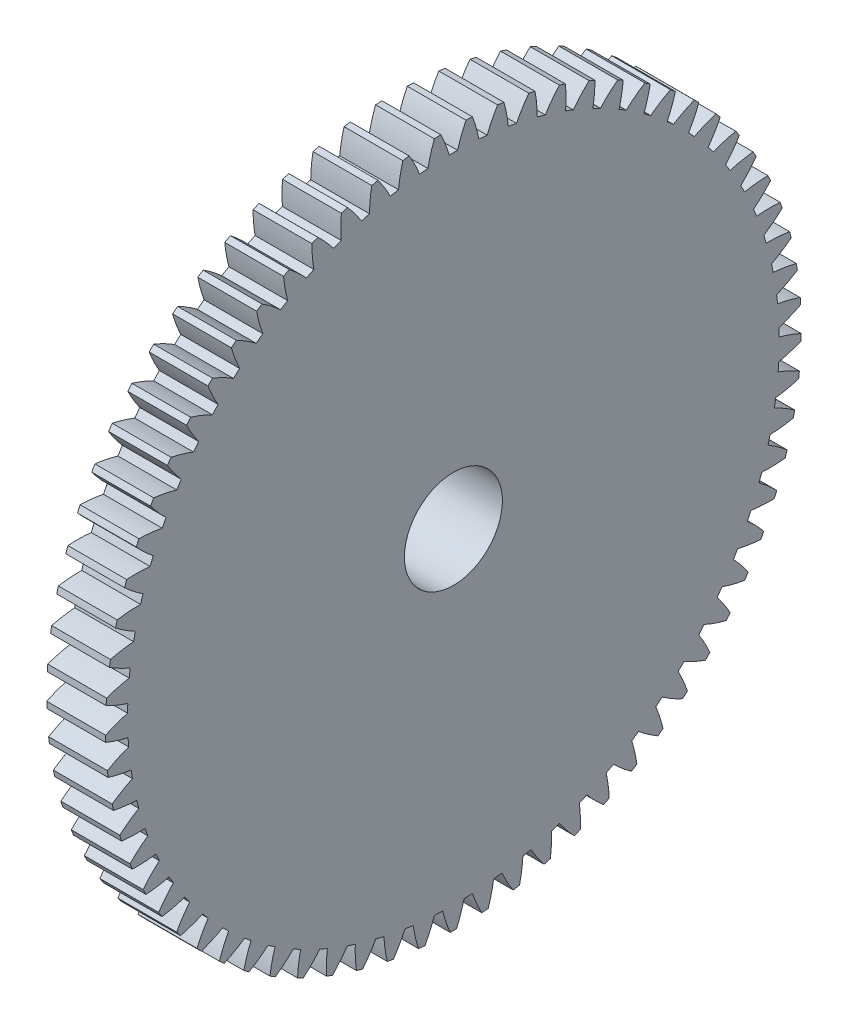
SolidWorks part; units mm, degrees
ref_plane "Plane1" through (0, 0, 0) normal (0, 0, 1) x (1, 0, 0)
ref_plane "Plane2" through (0, 0, 0) normal (0, 1, 0) x (1, 0, 0)
ref_plane "Plane3" through (0, 0, 0) normal (1, 0, 0) x (0, 0, -1)
sketch "HoldingSke" plane through (0, 0, 0) normal (0, 1, 0) x (1, 0, 0)
  line L0 (0, 0) -> (0.7167, -1.8672)
  line L1 (-15, 0) -> (100, 0) construction
  line L2 (0, 0) -> (-2.1039, 2.3779)
  line L3 (0, 0) -> (-11.863, 4.5341)
  line L4 (0, 0) -> (3.0949, 8.0624)
  line L5 (0, 0) -> (-4.6848, -1.7473)
  line L6 (0, 0) -> (-2.4869, -1.6779)
  line L7 (-2.1039, 2.3779) -> (-1.0276, 7.2607)
  line L8 (-76.2, 54.61) -> (-75.3, 54.61)
  line L9 (-71.009, 38.7566) -> (-53.1078, 45.2721)
  line L10 (-76.2, 71.12) -> (104.1128, 71.12)
  line L11 (0, 0) -> (-3, 0)
  line L12 (-76.2, 101.6) -> (-76.181, 101.6)
  line L13 (24.9733, 27.94) -> (52.9518, 28.4284)
  line L14 (24.9733, 27.94) -> (24.9743, 27.94)
  line L15 (24.9733, 27.94) -> (100.4006, 29.5858)
  line L16 (-63.627, -0.5) -> (-12.827, -0.5)
  circle A0 centre (0, 0) radius 2.5
  circle A1 centre (0, 0) radius 10
  circle A2 centre (0, 0) radius 10
  circle A3 centre (0, 0) radius 2.5
  dimension "MHD" = 20
  dimension "Hub_dia" = 20
  dimension "Bore" = 5
  dimension "MBD" = 5
  dimension "Num_teeth" = 69
  dimension "Pitch_radius" = 180.3128
  dimension "Pitch" = 2
  dimension "Width" = 3
  dimension "Overall_len" = 5
  dimension "Show_teeth" = 69
  dimension "Thickness" = 3
  dimension "OAL" = 5.0001
  dimension "T_dim" = 0.9
  dimension "Ap" = 20
  dimension "H" = 19.05
  dimension "Backlash" = 0.019
  dimension "Addendum_fac" = 1
  dimension "Dedendum_fac" = 1.25
  dimension "Clearance_fac" = 0.25
  dimension "Dedendum_add" = 0.001
  dimension "Module" = 0.5
sketch "BasProSke" plane through (0, 0, 0) normal (0, 1, 0) x (1, 0, 0)
  line L0 (-10, 0) -> (60, 0) construction
  line L1 (0, 0) -> (0, 17.75)
  line L2 (0, 0) -> (3, 0)
  line L3 (3, 0) -> (3, 17.75)
  line L4 (3, 17.75) -> (0, 17.75)
  dimension "Diameter" = 35.5
  dimension "Thickness" = 3
revolve "Base-Revolve" add sketch "BasProSke" angle 360 about L0
sketch "TooCutSke" plane through (0, 0, 0) normal (1, 0, 0) x (0, 0, -1)
  line L1 (0, 0) -> (0, 107) construction
  line L2 (0, 0) -> (-0.4259, 17.2447) construction
  line L3 (0, 0) -> (-1.5699, 34.4568) construction
  line L4 (-0.4259, 17.2447) -> (-0.785, 17.2284) construction
  arc A0 (0.2124, 16.6226) -> (-0.2124, 16.6226) centre (0, 0) ccw
  arc A1 (0.6571, 17.7633) -> (-0.6571, 17.7633) centre (0, 0) ccw
  circle A2 centre (0, 0) radius 17.25 construction
  circle A3 centre (0, 0) radius 16.2097 construction
  arc A4 (-0.2124, 16.6226) -> (-0.6571, 17.7633) centre (-6.8382, 14.6967) ccw
  arc A5 (0.6571, 17.7633) -> (0.2124, 16.6226) centre (6.8382, 14.6967) ccw
  dimension "Root_dia" = 33.248
  dimension "Overcut_dia" = 35.5508
  dimension "Pitch_dia" = 34.5
  dimension "Base_dia" = 32.4194
  dimension "Flank_rad" = 6.9
  dimension "Half_ang" = 2.609
  dimension "Half_CT" = 0.3594
extrude "ToothCut" cut sketch "TooCutSke" along normal through all
fillet "Breaks" [suppressed] radius 0.01
fillet "RootFillets" [suppressed] radius 0.126
pattern_circular "TeethCuts" count 69 every 5.217 about axis through (-10, 0, 0) along (1, 0, 0) of "ToothCut", "RootFillets", "Breaks"
sketch "HubNeaOneSke" plane through (0, 0, 0) normal (-1, 0, 0) x (0, 0, 1)
  circle A0 centre (0, 0) radius 10
  dimension "Diameter" = 20
extrude "HubNearOne" add sketch "HubNeaOneSke" along normal blind 2.0001
sketch "HubNeaBotSke" plane through (0, 0, 0) normal (-1, 0, 0) x (0, 0, 1)
  circle A0 centre (0, 0) radius 10
  dimension "Diameter" = 20
extrude "HubNearBoth" [suppressed] add sketch "HubNeaBotSke" along normal blind 1
ref_plane "FarPln" through (3, 0, 0) normal (1, 0, 0) x (0, 0, -1)
sketch "HubFarSke" plane through (3, 0, 0) normal (1, 0, 0) x (0, 0, -1)
  circle A0 centre (0, 0) radius 10
  dimension "Diameter" = 20
extrude "HubFar" [suppressed] add sketch "HubFarSke" along normal blind 1
sketch "BorSke" plane through (0, 0, 0) normal (1, 0, 0) x (0, 0, -1)
  circle A0 centre (0, 0) radius 2.5
  dimension "Diameter" = 5
extrude "Bore" cut sketch "BorSke" along normal mid plane 10.0001
sketch "KeySke" plane through (0, 0, 0) normal (1, 0, 0) x (0, 0, -1)
  line L0 (-1, 0) -> (-1, 3.4)
  line L1 (-1, 3.4) -> (1, 3.4)
  line L2 (1, 3.4) -> (1, 0)
  line L3 (0, 0) -> (0, 34) construction
  line L4 (-1, 0) -> (1, 0)
  dimension "Offset" = 3.4
  dimension "Width" = 2
extrude "Keyway" [suppressed] cut sketch "KeySke" along normal mid plane 10.0001
pattern_circular "Keyway2" [suppressed] count 2 every 90 about axis through (-10, 0, 0) along (1, 0, 0)
sketch "Sketch1" plane through (-2.0001, 0, 0) normal (-1, 0, 0) x (0, 0, 1)
  circle A0 centre (0, 0) radius 2.5
  circle A1 centre (0, 0) radius 4
extrude "Boss-Extrude1" add sketch "Sketch1" along normal blind 6
equation "' \"Module@HoldingSke\" = 6.35"
equation "' \"Num_teeth@HoldingSke\" = 12"
equation "' \"Ap@HoldingSke\" =  20"
equation "' \"Width@HoldingSke\" = 0.5 * 25.4"
equation "' \"Hub_dia@HoldingSke\"= 1 * 25.4"
equation "' \"Overall_len@HoldingSke\" = 1.0 * 25.4"
equation "' \"Bore@HoldingSke\" = 0.75 * 25.4"
equation "' \"T_dim@HoldingSke\" = 0.1 * 25.4"
equation "' \"Width@KeySke\" = 0.25 * 25.4"
equation "' \"Show_teeth@HoldingSke\" = 13"
equation "' \"Backlash@HoldingSke\" = 0.009 * 25.4"
equation "' \"Addendum_fac@HoldingSke\" = 1.0"
equation "' \"Dedendum_fac@HoldingSke\" = 1.25"
equation "' \"Dedendum_add@HoldingSke\" = 0.00005 * 25.4"
equation "' \"Clearance_fac@HoldingSke\" = 0.25"
equation "\"Pitch@HoldingSke\" = 1 / \"Module@HoldingSke\""
equation "\"Overcut_dia@TooCutSke\" = (\"Num_teeth@HoldingSke\" + 2 * \"Addendum_fac@HoldingSke\") / \"Pitch@HoldingSke\" + 0.002 * 25.4"
equation "\"Pitch_dia@TooCutSke\" = \"Num_teeth@HoldingSke\" / \"Pitch@HoldingSke\""
equation "\"Base_dia@TooCutSke\" = \"Num_teeth@HoldingSke\" / \"Pitch@HoldingSke\" * cos((\"Ap@HoldingSke\"  * 3.14159265 / 180))"
equation "\"Root_dia@TooCutSke\" = (\"Num_teeth@HoldingSke\" + 2) / \"Pitch@HoldingSke\" - 2 * (\"Addendum_fac@HoldingSke\" + \"Dedendum_fac@HoldingSke\") / \"Pitch@HoldingSke\" - \"Dedendum_add@HoldingSke\" * 2"
equation "\"Half_ang@TooCutSke\" = 180 / \"Num_teeth@HoldingSke\""
equation "\"Half_CT@TooCutSke\" = \"Num_teeth@HoldingSke\" / \"Pitch@HoldingSke\" * sin((3.14159265 / 2 / \"Num_teeth@HoldingSke\")) / 2 - 7 * \"Backlash@HoldingSke\" / 4"
equation "\"Flank_rad@TooCutSke\" = \"Num_teeth@HoldingSke\" / \"Pitch@HoldingSke\" / 5"
equation "\"Radius@RootFillets\" = \"Clearance_fac@HoldingSke\" / \"Pitch@HoldingSke\" + \"Dedendum_add@HoldingSke\""
equation "\"Break_rad@Breaks\" = 0.02 / \"Pitch@HoldingSke\""
equation "\"Thickness@HoldingSke\" = \"Width@HoldingSke\""
equation "\"OAL@HoldingSke\" = \"Thickness@HoldingSke\""
equation "\"MHD@HoldingSke\" = (\"Num_teeth@HoldingSke\" + 2) / \"Pitch@HoldingSke\" - 2 * (\"Addendum_fac@HoldingSke\" + \"Dedendum_fac@HoldingSke\")  / \"Pitch@HoldingSke\" - \"Dedendum_add@HoldingSke\" * 2"
equation "\"MBD@HoldingSke\" = (\"Num_teeth@HoldingSke\" + 2) / \"Pitch@HoldingSke\" - 2 * (\"Addendum_fac@HoldingSke\" + \"Dedendum_fac@HoldingSke\")  / \"Pitch@HoldingSke\" - \"Dedendum_add@HoldingSke\" * 2 - 0.002 * 25.4"
equation "\"MHD@HoldingSke\" = ((sgn( \"MHD@HoldingSke\" - \"Hub_dia@HoldingSke\" )-1)*( \"MHD@HoldingSke\" - \"Hub_dia@HoldingSke\" ))/-2+ \"Hub_dia@HoldingSke\""
equation "\"MBD@HoldingSke\" = ((sgn( \"MBD@HoldingSke\" - \"Bore@HoldingSke\" )-1)*( \"MBD@HoldingSke\" - \"Bore@HoldingSke\" ))/-2+ \"Bore@HoldingSke\""
equation "\"OAL@HoldingSke\" = ((sgn( \"OAL@HoldingSke\" - \"Overall_len@HoldingSke\" )+1)*( \"OAL@HoldingSke\" - \"Overall_len@HoldingSke\" ))/2 + \"Overall_len@HoldingSke\" + 0.000002 * 25.4"
equation "\"Num_teeth@TeethCuts\" = int( \"Show_teeth@HoldingSke\" ) + 1"
equation "\"Num_teeth@TeethCuts\" = ((sgn( \"Num_teeth@TeethCuts\" - \"Num_teeth@HoldingSke\" )-1)*( \"Num_teeth@TeethCuts\" - \"Num_teeth@HoldingSke\" ))/-2+ \"Num_teeth@HoldingSke\""
equation "\"Num_teeth@TeethCuts\" = ((sgn( \"Num_teeth@TeethCuts\" - 2.0)+1)*( \"Num_teeth@TeethCuts\" - 2.0))/2 +2.0"
equation "\"Angle@TeethCuts\" = 360.0 / \"Num_teeth@HoldingSke\""
equation "\"Diameter@BasProSke\" = (\"Num_teeth@HoldingSke\" + 2 * \"Addendum_fac@HoldingSke\") / \"Pitch@HoldingSke\""
equation "\"Thickness@BasProSke\"  = \"Thickness@HoldingSke\""
equation "' \"Fillet_rad@BasProSke\" =  \"Thickness@HoldingSke\" * 0.05"
equation "\"MHD@HoldingSke\" = ((sgn( \"MHD@HoldingSke\" - \"Root_dia@TooCutSke\" )-1)*( \"MHD@HoldingSke\" - \"Root_dia@TooCutSke\" ))/-2+ \"Root_dia@TooCutSke\""
equation "\"Diameter@HubNeaOneSke\" = \"MHD@HoldingSke\""
equation "\"Length@HubNearOne\" = \"OAL@HoldingSke\" - \"Thickness@BasProSke\""
equation "\"Diameter@HubNeaBotSke\" = \"MHD@HoldingSke\""
equation "\"Length@HubNearBoth\" = ( \"OAL@HoldingSke\" - \"Thickness@BasProSke\" ) / 2.0"
equation "\"Thickness@FarPln\" = \"Thickness@BasProSke\""
equation "\"Diameter@HubFarSke\" = \"MHD@HoldingSke\""
equation "\"Length@HubFar\" = ( \"OAL@HoldingSke\" - \"Thickness@BasProSke\" ) / 2.0"
equation "\"Diameter@BorSke\" = \"MBD@HoldingSke\""
equation "\"D1@Bore\" = \"OAL@HoldingSke\" * 2.0"
equation "\"D1@Keyway\" = \"OAL@HoldingSke\" * 2.0"
equation "\"Offset@KeySke\" = \"T_dim@HoldingSke\" + \"MBD@HoldingSke\" / 2.0"
